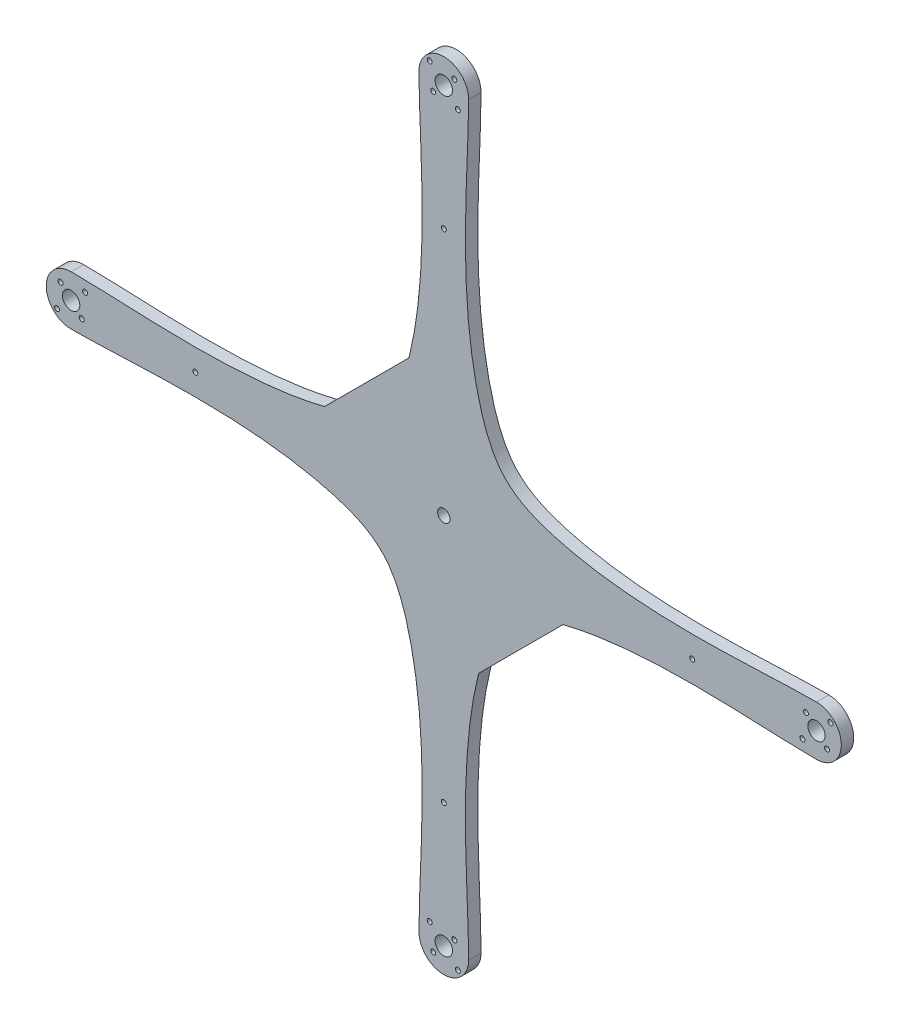
SolidWorks part; units mm, degrees
ref_plane "Front Plane" through (0, 0, 0) normal (0, 0, 1) x (1, 0, 0)
ref_plane "Top Plane" through (0, 0, 0) normal (0, 1, 0) x (1, 0, 0)
ref_plane "Right Plane" through (0, 0, 0) normal (1, 0, 0) x (0, 0, -1)
sketch "Sketch1" plane through (0, 0, 0) normal (0, 0, 1) x (1, 0, 0)
  line L0 (-150, 0) -> (0, 0) construction
  line L1 (0, 0) -> (150, 0) construction
  line L2 (0, 0) -> (0, -150) construction
  line L3 (0, 0) -> (0, 150) construction
  line L4 (50, 0) -> (0, 50) construction
  line L5 (0, 50) -> (-16.1612, 33.8388) construction
  line L6 (-50, 0) -> (0, -50) construction
  line L7 (0, -50) -> (50, 0) construction
  line L10 (-150, -10) -> (-130, -10) construction
  line L11 (-10, -150) -> (-10, -140) construction
  line L12 (-144.3431, 5.6569) -> (-155.6569, -5.6569) construction
  line L13 (-154.2426, 4.2426) -> (-145.7574, -4.2426) construction
  line L14 (-136, 0) -> (-101, 0) construction
  line L17 (1.6, -42.5) -> (-1.6, -32.5) construction
  line L30 (-136, 0) -> (-50, 0) construction
  line L151 (-37.5, 0) -> (-14, 0) construction
  line L152 (-37.5, 0) -> (-14, 0) construction
  line L174 (10.6066, 31.8198) -> (31.8198, 10.6066) construction
  line L178 (0, -130) -> (0, -37.5) construction
  line L184 (0, -84.6854) -> (-9.8172, -84.6854) construction
  line L212 (-1.6, -82.1854) -> (1.6, -87.1854) construction
  line L213 (-1.6, -87.1854) -> (1.6, -82.1854) construction
  line L225 (0, 0) -> (21.2132, 21.2132) construction
  line L226 (0, 0) -> (7.7782, 7.7782)
  line L227 (13.0815, 2.4749) -> (2.4749, 13.0815) construction
  line L228 (2.4749, 13.0815) -> (-13.0815, -2.4749) construction
  line L229 (-13.0815, -2.4749) -> (-2.4749, -13.0815) construction
  line L230 (-2.4749, -13.0815) -> (13.0815, 2.4749) construction
  line L235 (14, -48) -> (48, -14)
  line L236 (-48, 14) -> (-14, 48)
  line L237 (-33.8388, 16.1612) -> (-50, 0) construction
  arc A0 (-10, -150) -> (10, -150) centre (0, -150) ccw
  arc A1 (-150, 10) -> (-150, -10) centre (-150, 0) ccw
  arc A2 (10, 150) -> (-10, 150) centre (0, 150) ccw
  arc A3 (150, -10) -> (150, 10) centre (150, 0) ccw
  circle A5 centre (-155.6569, -5.6569) radius 1
  circle A6 centre (-144.3431, 5.6569) radius 1
  circle A7 centre (-145.7574, -4.2426) radius 1
  circle A8 centre (-154.2426, 4.2426) radius 1
  circle A9 centre (-5.6569, 155.6569) radius 1
  circle A10 centre (-4.2426, 145.7574) radius 1
  circle A11 centre (5.6569, 144.3431) radius 1
  circle A12 centre (4.2426, 154.2426) radius 1
  circle A13 centre (155.6569, 5.6569) radius 1
  circle A14 centre (145.7574, 4.2426) radius 1
  circle A15 centre (144.3431, -5.6569) radius 1
  circle A16 centre (154.2426, -4.2426) radius 1
  circle A17 centre (5.6569, -155.6569) radius 1
  circle A18 centre (4.2426, -145.7574) radius 1
  circle A19 centre (-5.6569, -144.3431) radius 1
  circle A20 centre (-4.2426, -154.2426) radius 1
  circle A25 centre (-150, 0) radius 3.5
  circle A26 centre (0, 150) radius 3.5
  circle A27 centre (150, 0) radius 3.5
  circle A28 centre (0, -150) radius 3.5
  circle A29 centre (0, 0) radius 37.5 construction
  circle A30 centre (0, 0) radius 2.5
  spline S0 degree 3 poles (-10, -150) (-10, -125.1194) (-3.9823, -72.8858) (-22.3124, -22.3138) (-72.8976, -3.9806) (-125.0121, -10) (-150, -10) knots 0 0 0 0 0.361155 0.451427 0.541698 0.902854 0.902854 0.902854 0.902854
  spline S1 degree 3 poles (-150, 10) (-125.1194, 10) (-83.3309, 5.1856) (-48, 14) knots 0 0 0 0 0.361155 0.361155 0.361155 0.361155
  spline S2 degree 3 poles (10, 150) (10, 125.1194) (3.9823, 72.8858) (22.3124, 22.3138) (72.8976, 3.9806) (125.0121, 10) (150, 10) knots 0 0 0 0 0.361155 0.451427 0.541698 0.902854 0.902854 0.902854 0.902854
  spline S3 degree 3 poles (150, -10) (125.1194, -10) (83.3309, -5.1856) (48, -14) knots 0 0 0 0 0.361155 0.361155 0.361155 0.361155
  spline S4 degree 3 poles (14, -48) (5.1843, -83.3189) (10, -125.0121) (10, -150) knots 0.541698 0.541698 0.541698 0.541698 0.902854 0.902854 0.902854 0.902854
  spline S5 degree 3 poles (-14, 48) (-5.1843, 83.3189) (-10, 125.0121) (-10, 150) knots 0.541698 0.541698 0.541698 0.541698 0.902854 0.902854 0.902854 0.902854
  point P2 (0, -37.5)
  point P14 (-150, 0)
  point P16 (0, 0)
  point P27 (-150, 0)
  point P46 (0, 0)
  point P77 (0, 0)
  point P78 (0, -37.5)
  point P88 (-118.5, 0)
  point P95 (0, 0)
  point P116 (-93, 0)
  point P118 (0, 0)
  point P138 (0, 0)
  point P141 (7.7782, 7.7782)
  point P221 (0, 0)
  point P228 (0, 0)
  point P229 (-25.75, 0)
  point P249 (0, 0)
  point P254 (21.2132, 21.2132)
  point P448 (0, 0)
  dimension "D2" = 20
  dimension "D3" = 4
  dimension "D9" = 2
  dimension "D14" = 7
  dimension "D16" = 75
  dimension "D21" = 5
  dimension "D24" = 15
  dimension "D13" = 0
  dimension "D1" = 300
  dimension "D5" = 20
  dimension "D6" = 10
  dimension "D7" = 16
  dimension "D8" = 12
  dimension "D11" = 35
  dimension "D18" = 5
  dimension "D19" = 3.2
  dimension "D22" = 11
  dimension "D23" = 30
  dimension "D25" = 22
  dimension "D10" = 4
  dimension "D15" = 4
extrude "Boss-Extrude2" add sketch "Sketch1" along normal blind 5
sketch "Sketch2" plane through (0, 0, 5) normal (0, 0, 1) x (1, 0, 0)
  line L0 (0, -150) -> (0, -100) construction
  circle A0 centre (0, -100) radius 1
  circle A1 centre (-100, 0) radius 1
  circle A2 centre (0, 100) radius 1
  circle A3 centre (100, 0) radius 1
  point P14 (0, 0)
  dimension "D2" = 2
  dimension "D1" = 50
  dimension "D3" = 4
extrude "Cut-Extrude1" cut sketch "Sketch2" against normal through all
